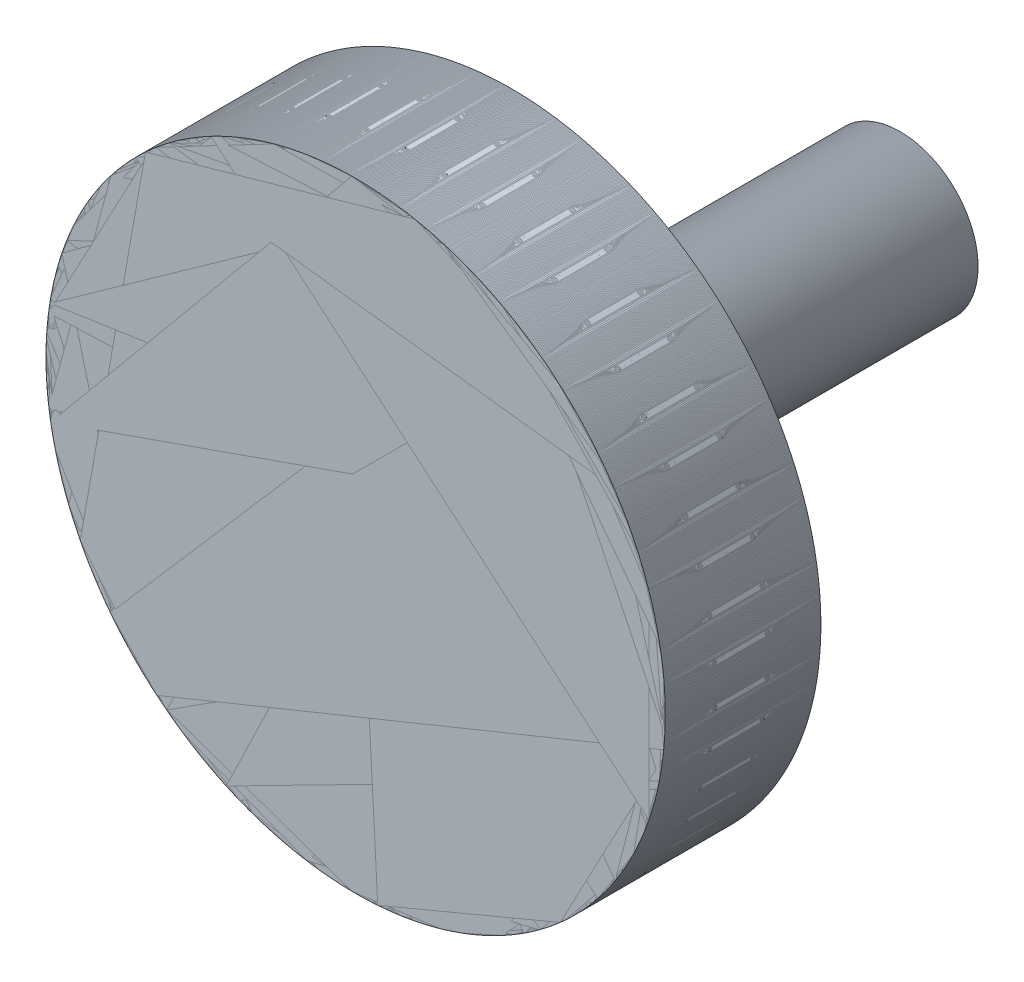
SolidWorks part; units mm, degrees
ref_plane "Спереди" through (0, 0, 0) normal (0, 0, 1) x (1, 0, 0)
ref_plane "Сверху" through (0, 0, 0) normal (0, 1, 0) x (1, 0, 0)
ref_plane "Справа" through (0, 0, 0) normal (1, 0, 0) x (0, 0, -1)
sketch "Эскиз1" plane through (0, 0, 0) normal (0, 0, 1) x (1, 0, 0)
  circle A0 centre (0, 0) radius 99.5
extrude "Бобышка-Вытянуть1" add sketch "Эскиз1" along normal blind 5
sketch "Эскиз2" plane through (0, 0, 5) normal (0, 0, 1) x (1, 0, 0)
  circle A0 centre (0, 0) radius 97.5
  circle A1 centre (0, 0) radius 99.5
extrude "Бобышка-Вытянуть3" add sketch "Эскиз2" along normal blind 40
sketch "Эскиз3" plane through (0, 0, 45) normal (0, 0, 1) x (1, 0, 0)
  circle A0 centre (0, 0) radius 99.5
extrude "Бобышка-Вытянуть4" add sketch "Эскиз3" along normal blind 5
sketch "Эскиз4" plane through (0, 0, 0) normal (0, 0, -1) x (-1, 0, 0)
  circle A0 centre (0, 0) radius 25
extrude "Бобышка-Вытянуть5" add sketch "Эскиз4" along normal blind 125
sketch "Эскиз5" plane through (0, 0, -125) normal (0, 0, -1) x (-1, 0, 0)
  circle A0 centre (0, 0) radius 22
extrude "Вырез-Вытянуть1" cut sketch "Эскиз5" against normal blind 135
sketch "Эскиз6" plane through (0, 0, 0) normal (0, 1, 0) x (1, 0, 0)
  line L0 (0, 0) -> (0, -73.9906) construction
  circle A0 centre (0, -17) radius 0.75
  circle A1 centre (0, -34) radius 0.75
  point P7 (0, 0)
  point P8 (0, 0)
extrude "Вырез-Вытянуть3" cut sketch "Эскиз6" against normal through all both and the other way through all
pattern_circular "Круговой массив1" count 25 over 360 about axis through (0, 0, 0) along (0, 0, 1) of bodies 108
fillet "Скругление1" radius 5 1 edges at (10.6445, -22.6207, 0)
